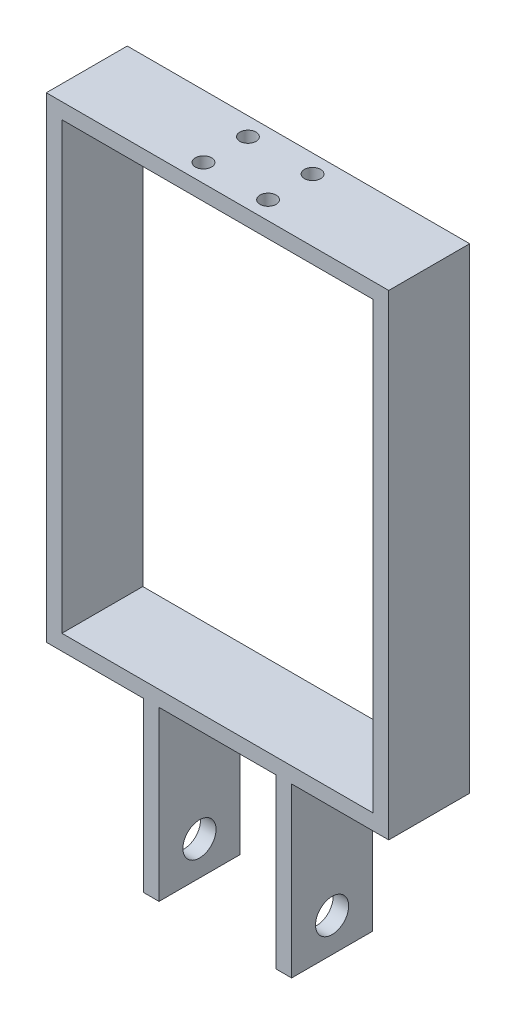
SolidWorks part; units mm, degrees
ref_plane "Front Plane" through (0, 0, 0) normal (0, 0, 1) x (1, 0, 0)
ref_plane "Top Plane" through (0, 0, 0) normal (0, 1, 0) x (1, 0, 0)
ref_plane "Right Plane" through (0, 0, 0) normal (1, 0, 0) x (0, 0, -1)
sketch "Sketch1" plane through (0, 0, 0) normal (0, 0, 1) x (1, 0, 0)
  line L0 (3.175, 34.29) -> (27.051, 34.29)
  line L1 (0, 0) -> (3.175, 0)
  line L2 (0, 0) -> (0, 34.29)
  line L4 (3.175, 0) -> (3.175, 34.29)
  line L5 (27.051, 34.29) -> (27.051, 0)
  line L6 (27.051, 0) -> (30.226, 0)
  line L7 (30.226, 0) -> (30.226, 34.29)
  line L8 (0, 34.29) -> (-19.812, 34.29)
  line L9 (-19.812, 34.29) -> (-19.812, 131.3688)
  line L10 (-19.812, 131.3688) -> (50.038, 131.3688)
  line L12 (46.863, 128.1938) -> (-16.637, 128.1938)
  line L13 (-16.637, 128.1938) -> (-16.637, 37.465)
  line L14 (-16.637, 37.465) -> (46.863, 37.465)
  line L15 (46.863, 37.465) -> (46.863, 128.1938)
  line L19 (50.038, 131.3688) -> (50.038, 34.29)
  line L20 (50.038, 34.29) -> (30.226, 34.29)
  point P10 (34.4177, 128.1938)
  point P13 (15.113, 128.1938)
  point P15 (0, 0)
  point P19 (38.7596, 131.3688)
  dimension "D1" = 34.29
  dimension "D2" = 3.175
  dimension "D3" = 23.876
  dimension "D4" = 90.7288
  dimension "D5" = 3.175
  dimension "D6" = 3.175
  dimension "D7" = 3.175
  dimension "D8" = 3.175
  dimension "D9" = 63.5
  dimension "D10" = 19.812
extrude "Boss-Extrude1" add sketch "Sketch1" along normal blind 16.51
sketch "Sketch2" plane through (0, 0, 0) normal (-1, 0, 0) x (0, 0, 1)
  line L0 (16.51, 0) -> (0, 0) construction
  circle A0 centre (8.255, 6.9215) radius 3.3782
  point P2 (0, 0)
  point P5 (8.255, 0)
  dimension "D1" = 6.7564
  dimension "D2" = 6.9215
extrude "Cut-Extrude1" cut sketch "Sketch2" against normal blind 42.672
sketch "Sketch3" plane through (0, 131.3688, 0) normal (0, 1, 0) x (1, 0, 0)
  line L0 (15.113, 0) -> (15.113, -16.51) construction
  line L1 (50.038, 0) -> (-19.812, 0) construction
  line L2 (50.038, -16.51) -> (-19.812, -16.51) construction
  line L3 (-19.812, -8.255) -> (50.038, -8.255) construction
  line L4 (-19.812, -16.51) -> (-19.812, 0) construction
  line L5 (50.038, -16.51) -> (50.038, 0) construction
  circle A0 centre (8.5238, -3.7182) radius 1.65
  circle A1 centre (8.5238, -12.7918) radius 1.65
  circle A2 centre (21.7022, -12.7918) radius 1.65
  circle A3 centre (21.7022, -3.7182) radius 1.65
  circle A4 centre (15.113, -8.255) radius 8
  point P20 (0, 0)
  point P21 (0, 0)
  point P22 (0, 0)
  dimension "D1" = 16
  dimension "D2" = 3.3
extrude "Cut-Extrude2" cut sketch "Sketch3" against normal blind 42.672 contours A4 A3 | A3 A4 | A4 A2 | A1 A4 | A4 A1 | A4 A0 | A0 A4 | A2 A4
